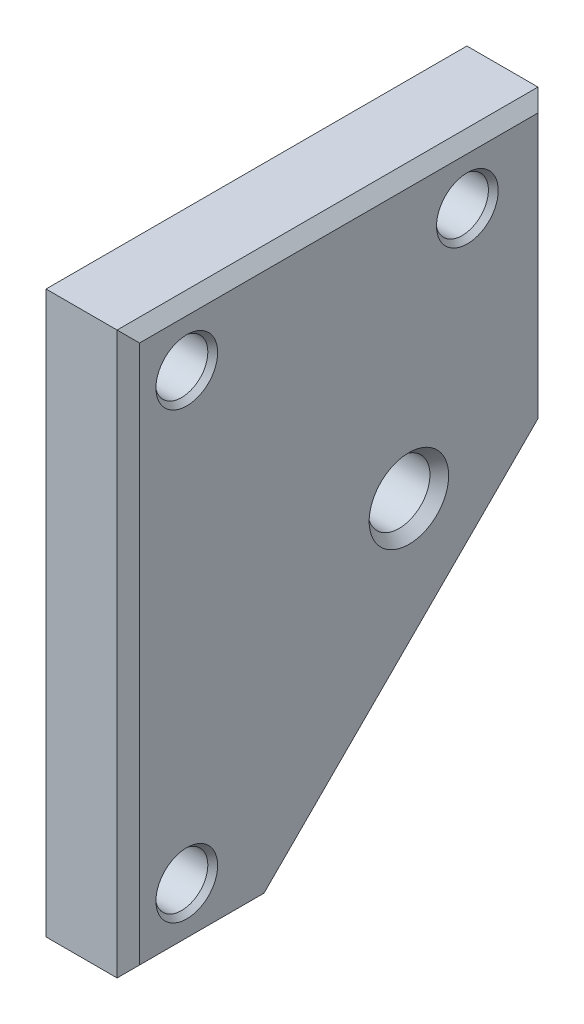
SolidWorks part; units mm, degrees
material "Plain Carbon Steel"
ref_plane "Front" through (0, 0, 0) normal (0, 0, 1) x (1, 0, 0)
ref_plane "Top" through (0, 0, 0) normal (0, 1, 0) x (1, 0, 0)
ref_plane "Right" through (0, 0, 0) normal (1, 0, 0) x (0, 0, -1)
sketch "Sketch1" plane through (0, 0, 0) normal (1, 0, 0) x (0, 0, -1)
  line L0 (-28.575, 0) -> (28.575, 0) construction
  line L1 (-28.575, 38.1) -> (28.575, 38.1)
  line L2 (-28.575, 38.1) -> (-28.575, -38.1)
  line L3 (-28.575, -38.1) -> (28.575, -38.1)
  line L4 (28.575, 38.1) -> (28.575, -38.1)
  dimension "D1" = 57.15
  dimension "D2" = 76.2
extrude "Extrude1" add sketch "Sketch1" along normal blind 12.7
hole_wizard "1/4 Clearance Hole1" positions "Sketch3" profile "Sketch2" hole size "1/4" standard "Ansi Inch" end condition up to next
sketch "Sketch3" plane through (12.7, 0, 0) normal (1, 0, 0) x (0, 0, -1)
  line L0 (-20.6375, 30.1625) -> (17.4625, 30.1625) construction
  line L3 (-20.6375, -30.1625) -> (17.4625, -30.1625) construction
  line L6 (-1.5875, 30.1625) -> (-1.5875, -30.1625) construction
  line L13 (-1.5875, 30.1625) -> (-1.5875, 38.1) construction
  line L14 (28.575, 38.1) -> (-28.575, 38.1) construction
  line L17 (-1.5875, -30.1625) -> (-1.5875, -38.1) construction
  line L18 (-28.575, -38.1) -> (28.575, -38.1) construction
  line L21 (-28.575, 38.1) -> (-28.575, -38.1) construction
  point P0 (-20.6375, 30.1625)
  point P1 (-20.6375, -30.1625)
  point P3 (17.4625, 30.1625)
  dimension "D1" = 60.325
  dimension "D2" = 38.1
  dimension "D3" = 7.9375
sketch "Sketch2" plane through (12.7, 30.1625, 20.6375) normal (0, 1, 0) x (0, 0, -1)
  line L0 (0, 0) -> (0, 12.7)
  line L1 (0, 12.7) -> (4.191, 12.7)
  line L2 (3.5712, 11.987) -> (3.5712, 0.713)
  line L3 (3.5712, 0.713) -> (4.191, 0)
  line L5 (4.191, 0) -> (0, 0)
  line L6 (-3.5712, 0.713) -> (-4.191, 0) construction
  line L7 (4.191, 12.7) -> (3.5712, 11.987)
  line L8 (-4.191, 12.7) -> (-3.5712, 11.987) construction
  line L11 (0, -6.35) -> (0, 107.95) construction
  dimension "Thru Hole Dia." = 7.1425
  dimension "Thru Hole Depth" = 12.7
  dimension "Near C'Sink Dia." = 8.382
  dimension "Near C'Sink Angle" = 82
  dimension "Far C'Sink Dia." = 8.382
  dimension "Far C'Sink Angle" = 82
hole_wizard "3/8-24 Tapped Hole1" positions "Sketch5" profile "Sketch4" tap size "3/8-24" standard "Ansi Inch" end condition up to next
sketch "Sketch5" plane through (12.7, 0, 0) normal (1, 0, 0) x (0, 0, -1)
  line L1 (-28.575, 38.1) -> (-28.575, -38.1) construction
  point P0 (9.525, 0)
  dimension "D1" = 38.1
cosmetic thread "Hole Thread1" parameters "D2"=9.525
sketch "Sketch4" plane through (12.7, 0, -9.525) normal (0, 1, 0) x (0, 0, -1)
  line L0 (0, 0) -> (0, 12.7)
  line L1 (0, 12.7) -> (5.3975, 12.7)
  line L2 (4.2164, 11.3413) -> (4.2164, 1.3587)
  line L3 (4.2164, 1.3587) -> (5.3975, 0)
  line L5 (5.3975, 0) -> (0, 0)
  line L6 (-4.2164, 1.3587) -> (-5.3975, 0) construction
  line L7 (5.3975, 12.7) -> (4.2164, 11.3413)
  line L8 (-5.3975, 12.7) -> (-4.2164, 11.3413) construction
  line L11 (0, -6.35) -> (0, 107.95) construction
  dimension "Thru Tap Drill Dia." = 8.4328
  dimension "Thru Tap Drill Depth" = 12.7
  dimension "Near C'Sink Dia." = 10.795
  dimension "Near C'Sink Angle" = 82
  dimension "Far C'Sink Dia." = 10.795
  dimension "Far C'Sink Angle" = 82
sketch "Sketch7" plane through (12.7, 0, 0) normal (1, 0, 0) x (0, 0, -1)
  line L1 (-9.525, -38.1) -> (28.575, 0)
  line L2 (-28.575, -38.1) -> (28.575, -38.1) construction
  line L3 (28.575, -38.1) -> (28.575, 38.1) construction
  line L4 (28.575, 0) -> (28.575, -38.1)
  line L7 (28.575, -38.1) -> (-9.525, -38.1)
  line L9 (-28.575, 38.1) -> (-28.575, -38.1) construction
  dimension "D1" = 19.05
extrude "Cut-Extrude2" cut sketch "Sketch7" against normal through all
chamfer "Chamfer1" distance 1.524 angle 45 10 edges at (0, -19.05, -9.525) (0, 19.05, -28.575) (0, 38.1, 0) (0, 0, 28.575) (0, -38.1, 19.05) (12.7, 19.05, -28.575) (12.7, -19.05, -9.525) (12.7, -38.1, 19.05) (12.7, 0, 28.575) (12.7, 38.1, 0)
